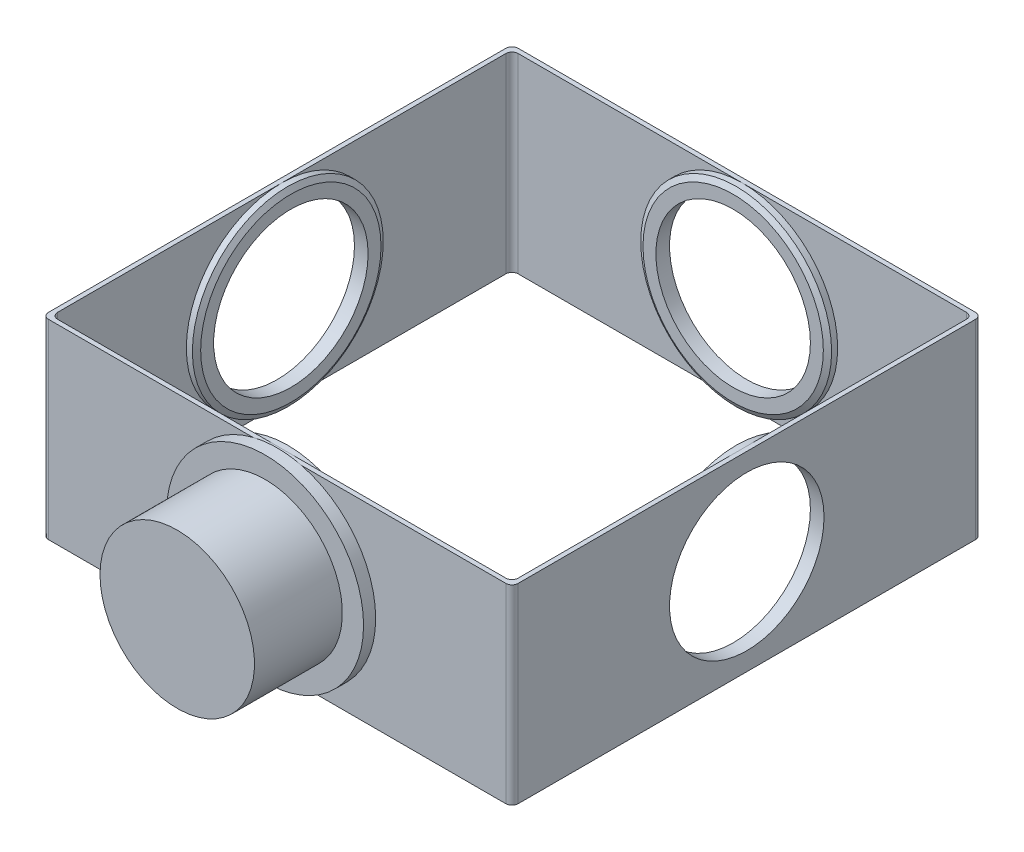
SolidWorks part; units mm, degrees
material "AISI Тип 316L нержавеющая сталь"
ref_plane "Спереди" through (0, 0, 0) normal (0, 0, 1) x (1, 0, 0)
ref_plane "Сверху" through (0, 0, 0) normal (0, 1, 0) x (1, 0, 0)
ref_plane "Справа" through (0, 0, 0) normal (1, 0, 0) x (0, 0, -1)
sketch "Эскиз1" plane through (0, 0, 0) normal (0, 1, 0) x (1, 0, 0)
  line L1 (2, 0) -> (153, 0)
  line L2 (0, 2) -> (0, 153)
  line L3 (2, 155) -> (153, 155)
  line L4 (155, 2) -> (155, 153)
  line L5 (3.5, 153.5) -> (151.5, 153.5)
  line L6 (1.5, 151.5) -> (1.5, 3.5)
  line L7 (3.5, 1.5) -> (151.5, 1.5)
  line L8 (153.5, 151.5) -> (153.5, 3.5)
  arc A0 (2, 0) -> (0, 2) centre (2, 2) cw
  arc A1 (1.5, 3.5) -> (3.5, 1.5) centre (3.5, 3.5) ccw
  arc A2 (153, 0) -> (155, 2) centre (153, 2) ccw
  arc A3 (151.5, 1.5) -> (153.5, 3.5) centre (151.5, 3.5) ccw
  arc A4 (153, 155) -> (155, 153) centre (153, 153) cw
  arc A5 (151.5, 153.5) -> (153.5, 151.5) centre (151.5, 151.5) cw
  arc A6 (0, 153) -> (2, 155) centre (2, 153) cw
  arc A7 (3.5, 153.5) -> (1.5, 151.5) centre (3.5, 151.5) ccw
  point P11 (0, 0)
  point P16 (155, 0)
  point P25 (0, 155)
  dimension "D7" = 2
  dimension "D1" = 155
  dimension "D2" = 155
  dimension "D3" = 1.5
  dimension "D4" = 1.5
  dimension "D5" = 1.5
  dimension "D6" = 1.5
extrude "Бобышка-Вытянуть1" add sketch "Эскиз1" along normal blind 63
sketch "Эскиз2" plane through (0, 0, 0) normal (0, 0, 1) x (1, 0, 0)
  line L0 (77.5, 63) -> (77.5, 0) construction
  line L1 (2, 63) -> (153, 63) construction
  line L2 (0, 31.5) -> (77.5, 31.5) construction
  line L3 (0, 63) -> (0, 0) construction
  circle A0 centre (77.5, 31.5) radius 25.5
  dimension "D1" = 51
extrude "Вырез-Вытянуть1" cut sketch "Эскиз2" against normal up to surface (155 mm away) up to face at (77.5, 31.5, -155)
sketch "Эскиз3" plane through (155, 0, 0) normal (1, 0, 0) x (0, 0, -1)
  line L0 (77.5, 63) -> (77.5, 0) construction
  line L1 (2, 63) -> (153, 63) construction
  line L2 (2, 0) -> (153, 0) construction
  line L3 (0, 31.5) -> (77.5, 31.5) construction
  line L4 (0, 63) -> (0, 0) construction
  circle A0 centre (77.5, 31.5) radius 25.5
  dimension "D1" = 51
extrude "Вырез-Вытянуть2" cut sketch "Эскиз3" against normal up to surface (155 mm away) up to face at (0, 31.5, -77.5)
sketch "Эскиз4" plane through (0, 0, -1.5) normal (0, 0, -1) x (-1, 0, 0)
  line L0 (-77.5, 63) -> (-77.5, 0) construction
  line L1 (-3.5, 63) -> (-151.5, 63) construction
  line L2 (-3.5, 0) -> (-151.5, 0) construction
  line L3 (-77.5, 31.5) -> (-42.2055, 31.5) construction
  circle A0 centre (-77.5, 31.5) radius 25.5
  circle A1 centre (-77.5, 31.5) radius 31.5
  dimension "D1" = 51
  dimension "D2" = 63
extrude "шайба1" add sketch "Эскиз4" along normal blind 3
chamfer "Фаска1 шайба" distance 1 angle 60 1 edges at (46, 31.5, -4.5)
sketch "Эскиз5" plane through (1.5, 0, 0) normal (1, 0, 0) x (0, 0, -1)
  line L0 (77.5, 63) -> (77.5, 0) construction
  line L1 (151.5, 63) -> (3.5, 63) construction
  line L2 (151.5, 0) -> (3.5, 0) construction
  line L3 (77.5, 31.5) -> (111.6807, 31.5) construction
  circle A0 centre (77.5, 31.5) radius 25.5
  circle A1 centre (77.5, 31.5) radius 31.5
  dimension "D1" = 51
  dimension "D2" = 63
extrude "Бобышка-Вытянуть4" add sketch "Эскиз5" along normal blind 3
chamfer "Фаска2" distance 1 angle 60 1 edges at (4.5, 31.5, -109)
sketch "Эскиз7" plane through (0, 0, -153.5) normal (0, 0, 1) x (1, 0, 0)
  line L0 (77.5, 63) -> (77.5, 0) construction
  line L1 (151.5, 63) -> (3.5, 63) construction
  line L2 (151.5, 0) -> (3.5, 0) construction
  line L3 (77.5, 31.5) -> (111.6807, 31.5) construction
  circle A0 centre (77.5, 31.5) radius 25.5
  circle A1 centre (77.5, 31.5) radius 31.5
  dimension "D1" = 51
  dimension "D2" = 63
sketch "Эскиз8" plane through (153.5, 0, 0) normal (-1, 0, 0) x (0, 0, 1)
  line L0 (-77.5, 63) -> (-77.5, 0) construction
  line L1 (-3.5, 63) -> (-151.5, 63) construction
  line L2 (-3.5, 0) -> (-151.5, 0) construction
  line L3 (-77.5, 31.5) -> (-38.3071, 31.5) construction
  circle A0 centre (-77.5, 31.5) radius 25.5
  circle A1 centre (-77.5, 31.5) radius 31.5
  dimension "D1" = 51
  dimension "D2" = 63
extrude "Бобышка-Вытянуть5" add sketch "Эскиз7" along normal blind 3
extrude "Бобышка-Вытянуть6" add sketch "Эскиз8" along normal blind 3
chamfer "Фаска3" distance 1 angle 60 2 edges at (109, 31.5, -150.5) (150.5, 31.5, -46)
sketch "Эскиз9" plane through (0, 0, 0) normal (0, 0, 1) x (1, 0, 0)
  line L0 (77.5, 63) -> (77.5, 0) construction
  line L1 (2, 0) -> (153, 0) construction
  line L2 (77.5, 31.5) -> (121.4267, 31.5) construction
  circle A0 centre (77.5, 31.5) radius 32.5
  dimension "D1" = 65
extrude "Бобышка-Вытянуть7" add sketch "Эскиз9" along normal blind 4
sketch "Эскиз10" plane through (0, 0, 4) normal (0, 0, 1) x (1, 0, 0)
  line L0 (77.5, 64) -> (77.5, -1) construction
  line L1 (77.5, 31.5) -> (119.3383, 31.5) construction
  circle A0 centre (77.5, 31.5) radius 32.5 construction
  circle A1 centre (77.5, 31.5) radius 25.5
  dimension "D1" = 51
extrude "Бобышка-Вытянуть8" add sketch "Эскиз10" along normal blind 29
equation "\"D4@Эскиз1\"=\"D3@Эскиз1\""
equation "\"D5@Эскиз1\"=\"D3@Эскиз1\""
equation "\"D6@Эскиз1\"=\"D3@Эскиз1\""
